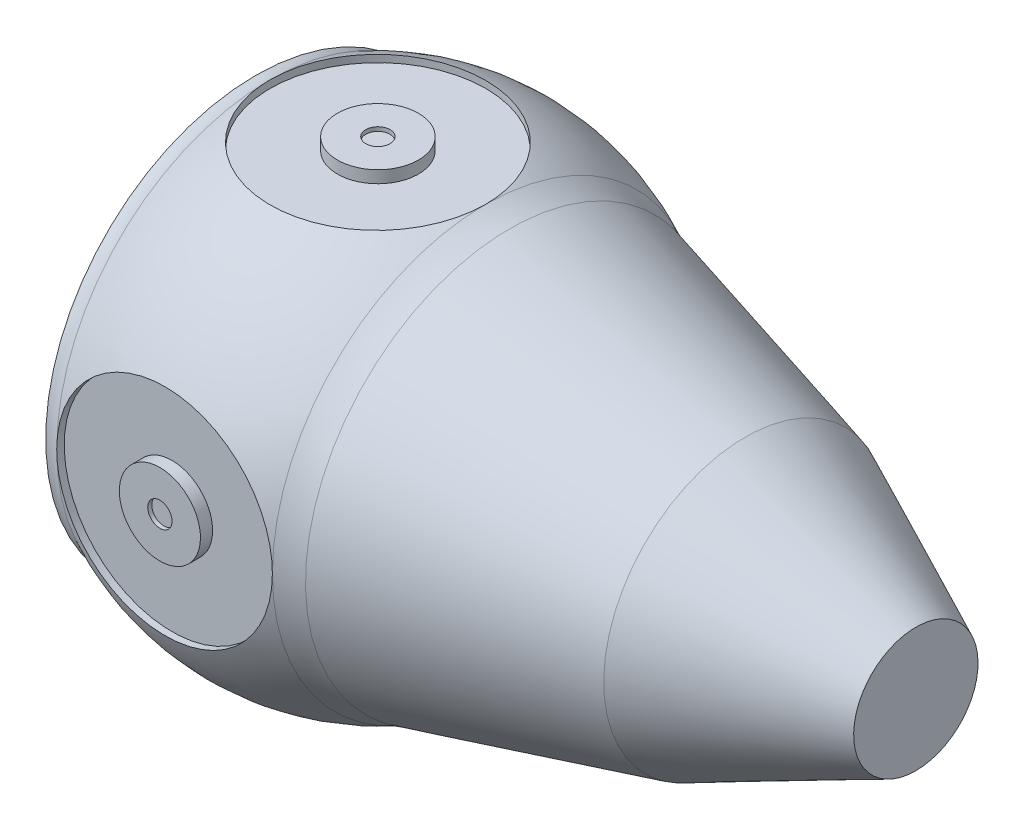
SolidWorks part; units mm, degrees
material "ABS"
ref_plane "Plano frontal" through (0, 0, 0) normal (0, 0, 1) x (1, 0, 0)
ref_plane "Plano superior" through (0, 0, 0) normal (0, 1, 0) x (1, 0, 0)
ref_plane "Plano direito" through (0, 0, 0) normal (1, 0, 0) x (0, 0, -1)
sketch "Esboço1" plane through (0, 0, 0) normal (0, 0, 1) x (1, 0, 0)
  line L0 (0, 0) -> (0, 2210.2124) construction
  line L1 (0, 0) -> (14.7458, 0) construction
  line L2 (3317.3997, 0) -> (3317.3997, 383.5)
  line L3 (3317.3997, 383.5) -> (2265.3997, 873)
  line L4 (2265.3997, 873) -> (813.3997, 1260)
  line L5 (0, -29.8386) -> (665, 1315.8122) construction
  line L6 (0, -29.8386) -> (-665, 1315.8122) construction
  line L7 (-753.6076, 1295.1127) -> (-1420, 1295.1127) construction
  line L8 (-3800.0045, 2216.6117) -> (-3800.0045, 0) construction
  line L9 (-14.7458, 0) -> (14.7458, 0) construction
  line L10 (-1420, 1295.1127) -> (-3610, 2160) construction
  line L11 (-3800.0045, 2216.6117) -> (-3794.1842, 2216.6117) construction
  line L12 (-3800.0045, 2326.7082) -> (-3925.0045, 2326.7082) construction
  line L13 (-1422.8547, 1280.1127) -> (-3618.2485, 2147.1301) construction
  line L14 (-6965, 15) -> (3302.3997, 15) construction
  line L15 (2260.2649, 858.8449) -> (809.5366, 1245.506) construction
  line L16 (-6630, 350) -> (2559.7577, 350) construction
  line L17 (-753.6076, 1280.1127) -> (-1422.8547, 1280.1127) construction
  line L18 (-4829, 2860) -> (-6980, 3864) construction
  line L19 (-4834.2705, 2845.9065) -> (-6965, 3840.4451) construction
  line L20 (-6980, 0) -> (3317.3997, 0) construction
  line L21 (-3925.0045, 0) -> (-3800.0045, 0) construction
  line L22 (3302.3997, 0) -> (-3800.0045, 0) construction
  line L23 (3302.3997, 373.9352) -> (2260.2649, 858.8449)
  line L24 (2260.2649, 858.8449) -> (1370.2011, 1096.0727)
  line L25 (-1333.8446, 1280.1127) -> (-1422.8547, 1280.1127) construction
  line L26 (-1422.8547, 1280.1127) -> (-3794.1842, 2216.6117) construction
  line L27 (-3925.0045, 2326.7082) -> (-3925.0045, 0) construction
  line L28 (-1333.8446, 1280.1127) -> (-753.6076, 945.1127) construction
  line L29 (723.2612, 921.8062) -> (813.3997, 946.0868) construction
  line L30 (3317.3997, 0) -> (3302.3997, 0)
  line L31 (-753.6076, 945.1127) -> (-1486.6089, 945.1127) construction
  line L32 (-1486.6089, 945.1127) -> (-3804.4893, 1860.5033) construction
  line L33 (-4951.2113, 2530.7942) -> (-6630, 3314.385) construction
  line L34 (-6630, 3314.385) -> (-6630, 350) construction
  line L35 (2145.5877, 542.715) -> (723.2612, 921.8062) construction
  line L36 (2559.7577, 350) -> (2145.5877, 542.715) construction
  line L37 (2559.7577, 350) -> (2559.7577, 350) construction
  line L38 (-6965, 3840.4451) -> (-6965, 15) construction
  line L39 (-6980, 3864) -> (-6980, 0) construction
  line L40 (3302.3997, 0) -> (3302.3997, 373.9352)
  line L41 (813.3997, 1260) -> (813.3997, 1244.4764) construction
  line L42 (3302.3997, 15) -> (3302.3997, 373.9352) construction
  line L43 (813.3997, 946.0868) -> (1370.2011, 1096.0727) construction
  line L44 (1370.2011, 1096.0727) -> (813.3997, 1244.4764)
  line L45 (813.3997, 1244.4764) -> (813.3997, 946.0868) construction
  line L46 (813.3997, 1244.4764) -> (55.0024, 1244.4764)
  line L47 (-753.6076, 1295.1127) -> (-753.6076, 1244.4764)
  line L48 (25.0024, 1244.4764) -> (25.0024, 1164.4764)
  line L49 (25.0024, 1164.4764) -> (55.0024, 1164.4764)
  line L50 (55.0024, 1164.4764) -> (55.0024, 1244.4764)
  line L51 (25.0024, 1244.4764) -> (-753.6076, 1244.4764)
  arc A0 (665, 1315.8122) -> (-665, 1315.8122) centre (0, -29.8386) ccw
  arc A1 (813.3997, 1260) -> (665, 1315.8122) centre (1019.4304, 2033.0145) cw
  arc A2 (-753.6076, 1295.1127) -> (-665, 1315.8122) centre (-753.6076, 1495.1127) ccw
  arc A3 (-3610, 2160) -> (-3800.0045, 2326.7082) centre (-5637.2528, 41.0847) ccw construction
  arc A4 (723.2612, 921.8062) -> (509.9367, 1002.0362) centre (1019.4304, 2033.0145) cw construction
  arc A5 (509.9367, 1002.0362) -> (-509.9367, 1002.0362) centre (0, -29.8386) ccw construction
  arc A6 (-753.6076, 945.1127) -> (-509.9367, 1002.0362) centre (-753.6076, 1495.1127) ccw construction
  arc A8 (658.3544, 1302.3646) -> (-658.3544, 1302.3646) centre (0, -29.8386) ccw construction
  arc A9 (-3618.2485, 2147.1301) -> (-4834.2705, 2845.9065) centre (-5637.2528, 41.0847) ccw construction
  arc A10 (-3610, 2160) -> (-4829, 2860) centre (-5637.2528, 41.0847) ccw construction
  arc A12 (-3804.4893, 1860.5033) -> (-4951.2113, 2530.7942) centre (-5637.2528, 41.0847) ccw construction
  arc A13 (809.5366, 1245.506) -> (658.3544, 1302.3646) centre (1019.4304, 2033.0145) cw construction
  arc A14 (-753.6076, 1280.1127) -> (-658.3544, 1302.3646) centre (-753.6076, 1495.1127) ccw construction
  point P17 (-4829, 2860)
  point P56 (-8569.7525, 41.0847)
  dimension "D1" = 800
  dimension "D7" = 1501
  dimension "D9" = 200
  dimension "D11" = 3610
  dimension "D14" = 2160
  dimension "D15" = 5865
  dimension "D2" = 767
  dimension "D3" = 1746
  dimension "D4" = 1052
  dimension "D5" = 2520
  dimension "D6" = 1452
  dimension "D8" = 1330
  dimension "D10" = 1420
  dimension "D12" = 4829
  dimension "D13" = 2860
  dimension "D16" = 5.8203
  dimension "D17" = 125
  dimension "D20" = 150
  dimension "D21" = 150
  dimension "D22" = 7242.4042
  dimension "D23" = 125
  dimension "D24" = 808.61
  dimension "D25" = 30
  dimension "D26" = 80
  dimension "D18" = 350
  dimension "D19" = 15
revolve "Revolução1" add sketch "Esboço1" angle 360 about L9
scale "Escala1" scale about origin uniform scaling yes scale factor 0.2
sketch "Esboço2" plane through (0, 0, 0) normal (0, 0, 1) x (1, 0, 0)
  line L0 (162.6799, 248.8953) -> (11.0005, 248.8953) construction
  line L2 (15, 268.8953) -> (15, 263.8953)
  line L3 (15, 263.8953) -> (0, 263.8953)
  line L4 (15, 268.8953) -> (50, 268.8953)
  line L5 (50, 268.8953) -> (50, 253.8953)
  line L6 (50, 253.8953) -> (133, 253.8953)
  line L7 (133, -263.1624) -> (133, 263.1624) construction
  line L8 (133, 253.8953) -> (133, 311.1464)
  line L11 (0, 311.1464) -> (133, 311.1464)
  line L12 (0, -141.1401) -> (0, 141.1401) construction
  line L13 (0, 263.8953) -> (0, 311.1464)
  point P20 (0, 0)
  dimension "D1" = 15
  dimension "D2" = 5
  dimension "D3" = 100
  dimension "D4" = 30
  dimension "D5" = 5
revolve "Corte-Revolução9" cut sketch "Esboço2" angle 360 about L12
hole_wizard "Rebaixo para parafuso Allen sextavado de M61" positions "Esboço8" profile "Esboço7" counterbore size "M6" standard "DIN"
sketch "Esboço8" plane through (0, 263.8953, 0) normal (0, 1, 0) x (1, 0, 0)
  point P0 (0, 0)
sketch "Esboço7" plane through (0, 263.8953, 0) normal (1, 0, 0) x (0, 0, 1)
  line L0 (0, 0) -> (0, 16.9828)
  line L1 (0, 16.9828) -> (3.3, 15)
  line L2 (3.3, 15) -> (3.3, 6.4)
  line L3 (3.3, 6.4) -> (5.5, 6.4)
  line L4 (5.5, 6.4) -> (5.5, 0)
  line L5 (5.5, 0) -> (0, 0)
  line L10 (0, 16.9828) -> (-3.3, 15) construction
  line L11 (0, -6.35) -> (0, 107.95) construction
  dimension "Hole Dia." = 6.6
  dimension "Hole Depth" = 15
  dimension "C'Bore Dia." = 11
  dimension "C'Bore Depth" = 6.4
  dimension "Drill Angle" = 118
pattern_circular "PadrãoCircular1" count 4 over 360 about axis through (0, 0, 0) along (1, 0, 0) of "Corte-Revolução9", "Rebaixo para parafuso Allen sextavado de M61"
hole_wizard "Furo com folga de M61" positions "Esboço9" profile "Esboço10" hole size "M6" standard "Ansi Metric"
sketch "Esboço9" plane through (11.0005, 0, 0) normal (1, 0, 0) x (0, 0, -1)
  line L0 (0, 248.8953) -> (0, 232.8953) construction
  point P9 (0, 240.8953)
  point P14 (240.8953, 0)
  point P15 (0, -240.8953)
  point P16 (-240.8953, 0)
  point P17 (0, 0)
sketch "Esboço10" plane through (11.0005, 240.8953, 0) normal (0, 1, 0) x (0, 0, -1)
  line L0 (0, 0) -> (0, 17.9823)
  line L1 (0, 17.9823) -> (3.3, 15.9995)
  line L2 (3.3, 15.9995) -> (3.3, 0)
  line L3 (3.3, 0) -> (0, 0)
  line L4 (0, 17.9823) -> (-3.3, 15.9995) construction
  line L5 (0, -6.35) -> (0, 107.95) construction
  dimension "Hole Dia." = 6.6
  dimension "Hole Depth" = 15.9995
  dimension "Drill Angle" = 118
